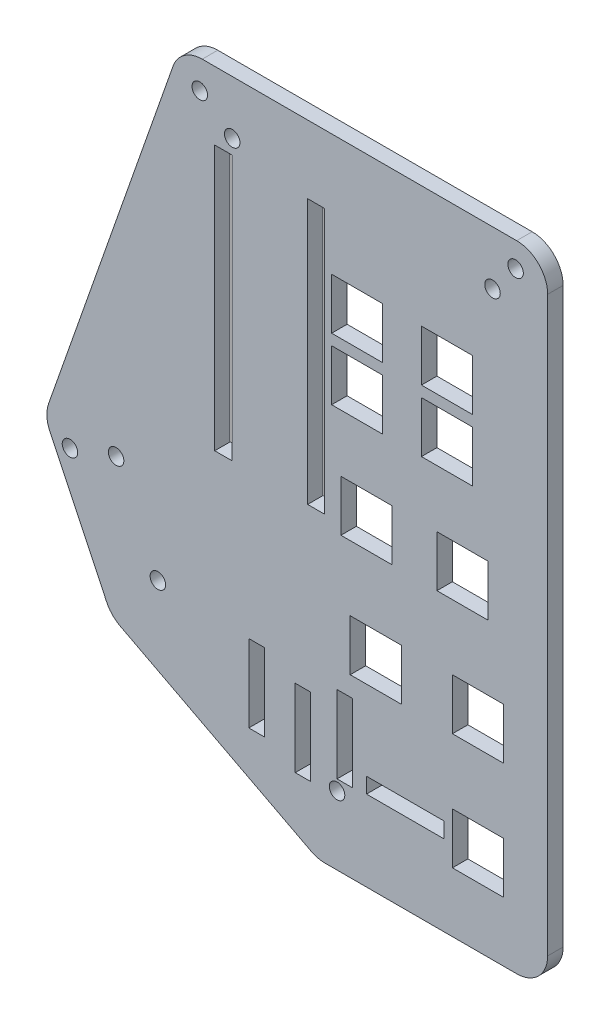
SolidWorks part; units mm, degrees
ref_plane "Front Plane" through (0, 0, 0) normal (0, 0, 1) x (1, 0, 0)
ref_plane "Top Plane" through (0, 0, 0) normal (0, 1, 0) x (1, 0, 0)
ref_plane "Right Plane" through (0, 0, 0) normal (1, 0, 0) x (0, 0, -1)
sketch "Sketch1" plane through (0, 0, 0) normal (0, 0, 1) x (1, 0, 0)
  line L6 (-20.066, -57.15) -> (46.99, -57.15) construction
  line L7 (-12.446, -73.152) -> (46.99, -73.152) construction
  line L8 (-3.3141, 6.35) -> (48.26, 6.35)
  line L9 (53.34, 1.27) -> (53.34, -92.71)
  line L10 (48.26, -97.79) -> (16.847, -97.79)
  line L16 (-8.1072, 2.9529) -> (-28.5162, -55.1739)
  line L18 (-20.066, -57.15) -> (-29.21, -57.15) construction
  line L26 (0, 0) -> (46.99, 0) construction
  line L27 (46.99, 0) -> (46.99, -88.9) construction
  line L28 (46.99, -88.9) -> (17.78, -88.9) construction
  line L29 (17.78, -88.9) -> (-12.446, -73.152) construction
  line L30 (-12.446, -73.152) -> (-20.066, -57.15) construction
  line L31 (-20.066, -57.15) -> (0, 0) construction
  line L32 (46.99, -57.15) -> (46.99, -88.9) construction
  line L33 (17.78, -88.9) -> (15.603, -97.79) construction
  line L34 (-12.446, -73.152) -> (-17.9301, -78.4424) construction
  line L35 (14.4997, -97.2152) -> (-16.7505, -80.9336)
  line L36 (-28.3096, -59.0409) -> (-18.9898, -78.6124)
  arc A0 (14.4997, -97.2152) -> (16.847, -97.79) centre (16.847, -92.71) ccw
  arc A1 (-28.5162, -55.1739) -> (-28.3096, -59.0409) centre (-23.723, -56.8568) ccw
  arc A2 (-16.7505, -80.9336) -> (-18.9898, -78.6124) centre (-14.4033, -76.4284) cw
  arc A3 (53.34, -92.71) -> (48.26, -97.79) centre (48.26, -92.71) cw
  arc A4 (48.26, 6.35) -> (53.34, 1.27) centre (48.26, 1.27) cw
  arc A5 (-8.1072, 2.9529) -> (-3.3141, 6.35) centre (-3.3141, 1.27) cw
  circle A6 centre (48.0822, 2.286) radius 1.27
  circle A7 centre (-3.7187, 1.651) radius 1.27
  circle A8 centre (-25.0123, -59.762) radius 1.27
  point P25 (53.34, -97.79)
  point P28 (53.34, 6.35)
  dimension "D11" = 5.2578
  dimension "D8" = 5.08
  dimension "D9" = 2.54
  dimension "D1" = 88.9
  dimension "D2" = 29.21
  dimension "D3" = 59.436
  dimension "D4" = 67.056
  dimension "D5" = 104.14
  dimension "D6" = 82.55
  dimension "D7" = 46.99
  dimension "D10" = 4.064
  dimension "D12" = 4.699
  dimension "D13" = 103.76
  dimension "D14" = 4.572
  dimension "D15" = 4.826
  dimension "D16" = 2.667
  dimension "D17" = 108.51
extrude "Boss-Extrude1" add sketch "Sketch1" along normal blind 2.54
sketch "Sketch3" plane through (0, 0, 2.54) normal (0, 0, 1) x (1, 0, 0)
  line L0 (46.99, -88.9) -> (0, -88.9) construction
  line L6 (-20.066, -57.15) -> (46.99, -57.15) construction
  line L7 (-12.446, -73.152) -> (46.99, -73.152) construction
  line L8 (0, 0) -> (46.99, 0) construction
  line L9 (46.99, 0) -> (46.99, -88.9) construction
  line L10 (46.99, -88.9) -> (17.78, -88.9) construction
  line L11 (17.78, -88.9) -> (-12.446, -73.152) construction
  line L12 (-12.446, -73.152) -> (-20.066, -57.15) construction
  line L13 (-20.066, -57.15) -> (0, 0) construction
sketch "Sketch5" plane through (0, 0, 0) normal (0, 0, -1) x (-1, 0, 0)
  line L0 (-46.99, 0) -> (-46.99, -17.78) construction
  line L1 (-46.99, 0) -> (-1.524, 0) construction
  line L2 (-46.99, -17.78) -> (-36.83, -17.78) construction
  line L3 (-46.99, 0) -> (-46.99, -27.94) construction
  line L8 (-41.021, -13.589) -> (-32.639, -13.589)
  line L9 (-41.021, -13.589) -> (-41.021, -21.971)
  line L10 (-46.99, 0) -> (-46.99, -45.72) construction
  line L15 (-41.021, -21.971) -> (-32.639, -21.971)
  line L16 (-32.639, -13.589) -> (-32.639, -21.971)
  line L17 (-46.99, 0) -> (-46.99, -88.9) construction
  line L18 (-46.99, -45.72) -> (-39.37, -45.72) construction
  line L19 (-41.021, -13.589) -> (-32.639, -21.971) construction
  line L20 (-46.99, 0) -> (-46.99, -64.77) construction
  line L21 (-43.561, -41.529) -> (-35.179, -41.529)
  line L22 (-43.561, -41.529) -> (-43.561, -49.911)
  line L23 (-43.561, -49.911) -> (-35.179, -49.911)
  line L24 (-35.179, -41.529) -> (-35.179, -49.911)
  line L25 (-43.561, -41.529) -> (-35.179, -49.911) construction
  line L26 (-43.561, -49.911) -> (-35.179, -41.529) construction
  line L27 (-46.99, -64.77) -> (-41.91, -64.77) construction
  line L28 (-41.021, -21.971) -> (-32.639, -13.589) construction
  line L29 (-46.99, -27.94) -> (-36.83, -27.94) construction
  line L30 (-46.99, 0) -> (-46.99, -83.82) construction
  line L31 (-41.021, -23.749) -> (-32.639, -23.749)
  line L32 (-41.021, -23.749) -> (-41.021, -32.131)
  line L33 (-41.021, -32.131) -> (-32.639, -32.131)
  line L34 (-32.639, -23.749) -> (-32.639, -32.131)
  line L35 (-41.021, -23.749) -> (-32.639, -32.131) construction
  line L36 (-41.021, -32.131) -> (-32.639, -23.749) construction
  line L37 (-46.101, -60.579) -> (-37.719, -60.579)
  line L38 (-46.101, -60.579) -> (-46.101, -68.961)
  line L39 (-46.101, -68.961) -> (-37.719, -68.961)
  line L40 (-37.719, -60.579) -> (-37.719, -68.961)
  line L41 (-46.101, -60.579) -> (-37.719, -68.961) construction
  line L42 (-46.101, -68.961) -> (-37.719, -60.579) construction
  line L43 (-46.99, -83.82) -> (-41.91, -83.82) construction
  line L44 (-36.83, -17.78) -> (-22.098, -17.78) construction
  line L45 (-46.101, -79.629) -> (-37.719, -79.629)
  line L46 (-46.101, -79.629) -> (-46.101, -88.011)
  line L47 (-46.101, -88.011) -> (-37.719, -88.011)
  line L48 (-37.719, -79.629) -> (-37.719, -88.011)
  line L49 (-46.101, -79.629) -> (-37.719, -88.011) construction
  line L50 (-46.101, -88.011) -> (-37.719, -79.629) construction
  line L51 (-36.83, -27.94) -> (-22.098, -27.94) construction
  line L52 (-39.37, -45.72) -> (-23.622, -45.72) construction
  line L53 (-41.91, -64.77) -> (-25.146, -64.77) construction
  line L54 (-46.99, 0) -> (-16.764, 0) construction
  line L55 (-26.289, -13.589) -> (-17.907, -13.589)
  line L56 (-26.289, -13.589) -> (-26.289, -21.971)
  line L57 (-26.289, -21.971) -> (-17.907, -21.971)
  line L58 (-17.907, -13.589) -> (-17.907, -21.971)
  line L59 (-26.289, -13.589) -> (-17.907, -21.971) construction
  line L60 (-26.289, -21.971) -> (-17.907, -13.589) construction
  line L61 (-26.289, -23.749) -> (-17.907, -23.749)
  line L62 (-26.289, -23.749) -> (-26.289, -32.131)
  line L63 (-26.289, -32.131) -> (-17.907, -32.131)
  line L64 (-17.907, -23.749) -> (-17.907, -32.131)
  line L65 (-26.289, -23.749) -> (-17.907, -32.131) construction
  line L66 (-26.289, -32.131) -> (-17.907, -23.749) construction
  line L67 (-27.813, -41.529) -> (-19.431, -41.529)
  line L68 (-27.813, -41.529) -> (-27.813, -49.911)
  line L69 (-27.813, -49.911) -> (-19.431, -49.911)
  line L70 (-19.431, -41.529) -> (-19.431, -49.911)
  line L71 (-27.813, -41.529) -> (-19.431, -49.911) construction
  line L72 (-27.813, -49.911) -> (-19.431, -41.529) construction
  line L73 (-29.337, -60.579) -> (-20.955, -60.579)
  line L74 (-29.337, -60.579) -> (-29.337, -68.961)
  line L75 (-29.337, -68.961) -> (-20.955, -68.961)
  line L76 (-20.955, -60.579) -> (-20.955, -68.961)
  line L77 (-29.337, -60.579) -> (-20.955, -68.961) construction
  line L78 (-29.337, -68.961) -> (-20.955, -60.579) construction
  line L79 (0, 0) -> (-46.99, 0) construction
  line L80 (-16.764, 0) -> (-16.764, -4.826) construction
  line L81 (-46.99, 0) -> (-13.97, 0) construction
  line L82 (-13.97, 0) -> (-13.97, -4.826) construction
  line L83 (-1.524, 0) -> (-1.524, -4.826) construction
  line L84 (-46.99, 0) -> (-17.1256, 0) construction
  line L85 (-1.524, 0) -> (-1.524, -48.26) construction
  line L86 (-46.99, 0) -> (1.27, 0) construction
  line L87 (1.27, 0) -> (1.27, -4.826) construction
  line L88 (-16.764, 0) -> (-16.764, -48.26) construction
  line L90 (-16.764, -4.826) -> (-13.97, -4.826)
  line L91 (-16.764, -4.826) -> (-16.764, -48.26)
  line L92 (-16.764, -48.26) -> (-13.97, -48.26)
  line L93 (-13.97, -4.826) -> (-13.97, -48.26)
  line L94 (-1.524, -4.826) -> (1.27, -4.826)
  line L95 (-1.524, -4.826) -> (-1.524, -48.26)
  line L96 (-1.524, -48.26) -> (1.27, -48.26)
  line L97 (1.27, -4.826) -> (1.27, -48.26)
  dimension "D2" = 8.382
  dimension "D3" = 64.77
  dimension "D4" = 8.382
  dimension "D5" = 10.16
  dimension "D6" = 17.78
  dimension "D7" = 8.382
  dimension "D8" = 8.382
  dimension "D9" = 45.72
  dimension "D10" = 7.62
  dimension "D11" = 8.382
  dimension "D12" = 8.382
  dimension "D13" = 27.94
  dimension "D14" = 10.16
  dimension "D15" = 5.08
  dimension "D16" = 8.382
  dimension "D17" = 8.382
  dimension "D18" = 8.382
  dimension "D19" = 8.382
  dimension "D20" = 83.82
  dimension "D21" = 5.08
  dimension "D22" = 8.382
  dimension "D23" = 8.382
  dimension "D24" = 14.732
  dimension "D25" = 8.382
  dimension "D26" = 8.382
  dimension "D27" = 14.732
  dimension "D28" = 8.382
  dimension "D29" = 8.382
  dimension "D30" = 15.748
  dimension "D31" = 8.382
  dimension "D32" = 8.382
  dimension "D33" = 16.764
  dimension "D34" = 30.226
  dimension "D35" = 4.826
  dimension "D36" = 33.02
  dimension "D37" = 4.826
  dimension "D38" = 45.466
  dimension "D39" = 4.826
  dimension "D40" = 48.26
  dimension "D41" = 4.826
  dimension "D42" = 48.26
  dimension "D43" = 48.26
extrude "Cut-Extrude1" cut sketch "Sketch5" against normal through all
sketch "Sketch7" plane through (0, 0, 2.54) normal (0, 0, 1) x (1, 0, 0)
  line L0 (46.99, 0) -> (44.2976, 0) construction
  line L1 (0, 0) -> (46.99, 0) construction
  line L2 (44.2976, 0) -> (44.2976, -2.4892) construction
  line L3 (46.99, 0) -> (1.6002, 0) construction
  line L4 (1.6002, 0) -> (1.6002, -2.4384) construction
  line L5 (-20.066, -57.15) -> (-17.4498, -57.15) construction
  line L6 (-20.066, -57.15) -> (46.99, -57.15) construction
  line L7 (-12.446, -73.152) -> (-10.5918, -73.152) construction
  line L8 (-12.446, -73.152) -> (46.99, -73.152) construction
  line L9 (-10.5918, -73.152) -> (-10.5918, -71.3486) construction
  line L10 (17.78, -88.9) -> (17.78, -86.5378) construction
  line L11 (17.78, -86.5378) -> (18.796, -86.5378) construction
  circle A0 centre (44.2976, -2.4892) radius 1.27
  circle A1 centre (1.6002, -2.4384) radius 1.27
  circle A2 centre (-17.4498, -57.15) radius 1.27
  circle A3 centre (-10.5918, -71.3486) radius 1.27
  circle A4 centre (18.796, -86.5378) radius 1.27
  dimension "D3" = 2.54
  dimension "D6" = 2.54
  dimension "D8" = 2.54
  dimension "D11" = 2.54
  dimension "D14" = 2.54
  dimension "D1" = 2.6924
  dimension "D2" = 2.4892
  dimension "D4" = 45.3898
  dimension "D5" = 2.4384
  dimension "D7" = 2.6162
  dimension "D9" = 1.8542
  dimension "D10" = 1.8034
  dimension "D12" = 2.3622
  dimension "D13" = 1.016
extrude "Cut-Extrude3" cut sketch "Sketch7" against normal through all
sketch "Sketch8" plane through (0, 0, 2.54) normal (0, 0, 1) x (1, 0, 0)
  line L0 (23.622, -82.042) -> (36.322, -82.042)
  line L1 (23.622, -82.042) -> (23.622, -84.582)
  line L2 (23.622, -84.582) -> (36.322, -84.582)
  line L3 (36.322, -82.042) -> (36.322, -84.582)
  line L4 (18.796, -72.136) -> (21.336, -72.136)
  line L5 (18.796, -72.136) -> (18.796, -84.836)
  line L6 (18.796, -84.836) -> (21.336, -84.836)
  line L7 (21.336, -72.136) -> (21.336, -84.836)
  line L8 (11.938, -74.676) -> (14.478, -74.676)
  line L9 (11.938, -74.676) -> (11.938, -87.376)
  line L10 (11.938, -87.376) -> (14.478, -87.376)
  line L11 (14.478, -74.676) -> (14.478, -87.376)
  line L12 (4.318, -72.136) -> (6.858, -72.136)
  line L13 (4.318, -72.136) -> (4.318, -84.836)
  line L14 (4.318, -84.836) -> (6.858, -84.836)
  line L15 (6.858, -72.136) -> (6.858, -84.836)
  line L16 (46.99, -83.312) -> (36.322, -83.312) construction
  line L17 (46.99, 0) -> (46.99, -88.9) construction
  line L18 (36.322, -83.312) -> (36.322, 0) construction
  line L19 (0, 0) -> (46.99, 0) construction
  line L20 (21.336, -72.136) -> (46.99, -72.136) construction
  line L21 (21.336, -72.136) -> (21.336, 0) construction
  line L22 (6.858, -72.136) -> (46.99, -72.136) construction
  line L23 (14.478, -74.676) -> (46.99, -74.676) construction
  line L24 (14.478, -74.676) -> (14.478, 0) construction
  line L25 (6.858, -72.136) -> (6.858, 0) construction
  dimension "D1" = 12.7
  dimension "D2" = 2.54
  dimension "D3" = 12.7
  dimension "D4" = 2.54
  dimension "D5" = 12.7
  dimension "D6" = 2.54
  dimension "D7" = 12.7
  dimension "D8" = 2.54
  dimension "D9" = 10.668
  dimension "D10" = 83.312
  dimension "D11" = 25.654
  dimension "D12" = 72.136
  dimension "D13" = 32.512
  dimension "D14" = 74.676
  dimension "D15" = 40.132
  dimension "D16" = 72.136
extrude "Cut-Extrude4" cut sketch "Sketch8" against normal through all
